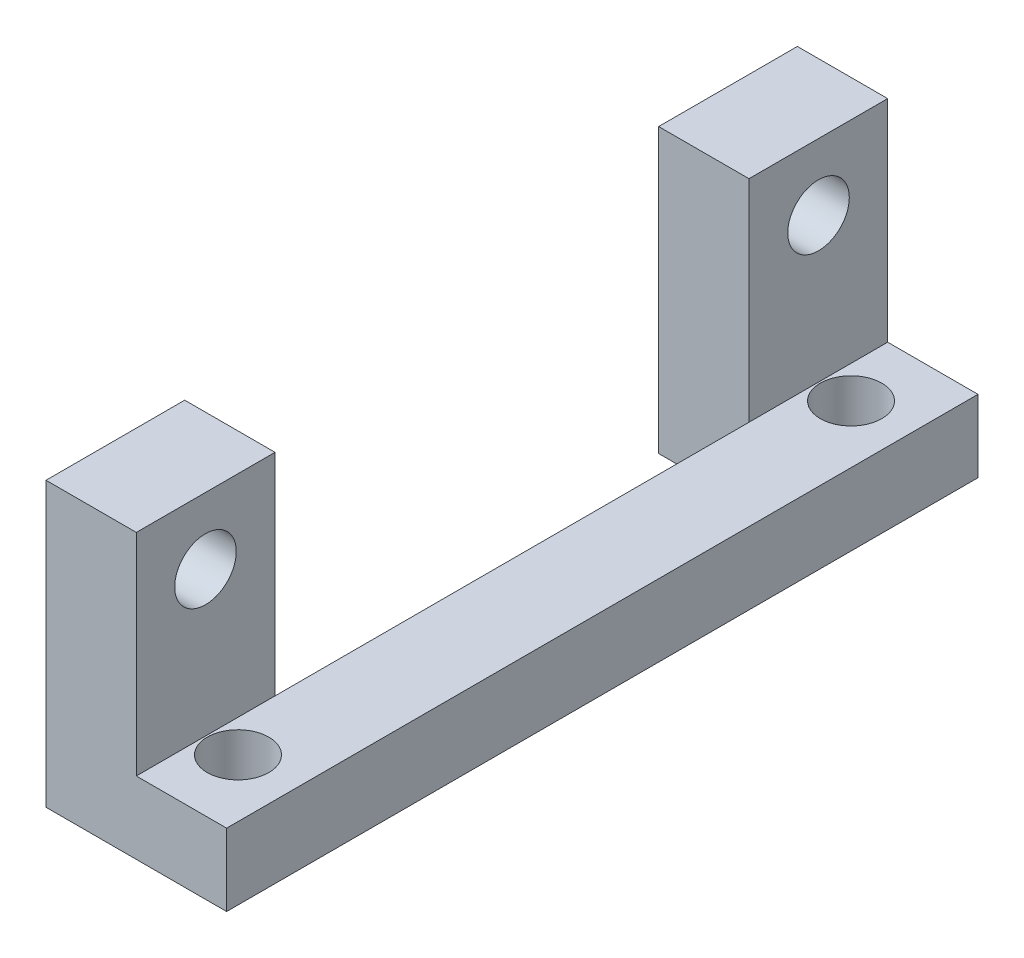
SolidWorks part; units mm, degrees
material "6061 Alloy"
ref_plane "Front Plane" through (0, 0, 0) normal (0, 0, 1) x (1, 0, 0)
ref_plane "Top Plane" through (0, 0, 0) normal (0, 1, 0) x (1, 0, 0)
ref_plane "Right Plane" through (0, 0, 0) normal (1, 0, 0) x (0, 0, -1)
sketch "Sketch1" plane through (0, 0, 0) normal (0, 0, 1) x (1, 0, 0)
  line L0 (0, 12.446) -> (0, 0)
  line L1 (0, 0) -> (7.9375, 0)
  line L2 (7.9375, 0) -> (7.9375, 3.175)
  line L3 (7.9375, 3.175) -> (3.9688, 3.175)
  line L4 (3.9688, 3.175) -> (3.9688, 12.446)
  line L5 (3.9688, 12.446) -> (0, 12.446)
  dimension "D1" = 12.446
  dimension "D2" = 7.9375
  dimension "D3" = 3.9688
  dimension "D4" = 3.175
extrude "Boss-Extrude1" add sketch "Sketch1" along normal mid plane 33.02
sketch "Sketch2" plane through (0, 12.446, 0) normal (0, 1, 0) x (1, 0, 0)
  line L0 (0, -16.51) -> (0, 16.51) construction
  line L1 (0, 10.414) -> (3.9688, 10.414)
  line L2 (0, 10.414) -> (0, -10.414)
  line L3 (0, -10.414) -> (3.9688, -10.414)
  line L4 (3.9688, 10.414) -> (3.9688, -10.414)
  line L5 (3.9688, -16.51) -> (3.9688, 16.51) construction
  dimension "D1" = 20.828
  dimension "D2" = 10.414
extrude "Cut-Extrude1" cut sketch "Sketch2" against normal up to next
hole_wizard "#6-32 Tapped Hole1" positions "Sketch4" profile "Sketch3" tap size "#6-32" standard "Ansi Inch" end condition up to next
sketch "Sketch4" plane through (3.9688, 0, 0) normal (1, 0, 0) x (0, 0, -1)
  line L0 (0, 0) -> (0, 22.9954) construction
  line L1 (0, 22.9954) -> (13.4704, 9.525) construction
  line L2 (0, 22.9954) -> (-13.4704, 9.525) construction
  line L3 (-16.51, 0) -> (16.51, 0) construction
  point P0 (-13.4704, 9.525)
  point P17 (13.4704, 9.525)
  dimension "D1" = 9.525
  dimension "D2" = 19.05
  dimension "D3" = 19.05
sketch "Sketch3" plane through (3.9688, 9.525, 13.4704) normal (0, 1, 0) x (0, 0, -1)
  line L0 (0, 0) -> (0, 3.9688)
  line L1 (0, 3.9688) -> (1.3525, 3.9688)
  line L2 (1.3525, 3.9688) -> (1.3525, 0)
  line L5 (1.3525, 0) -> (0, 0)
  line L11 (0, -6.35) -> (0, 107.95) construction
  dimension "Thread Major Dia." = 2.7051
  dimension "Thru Tap Drill Depth" = 3.9688
hole_wizard "#6-32 Tapped Hole2" positions "Sketch6" profile "Sketch5" tap size "#6-32" standard "Ansi Inch" end condition up to next
sketch "Sketch6" plane through (0, 0, 0) normal (0, -1, 0) x (1, 0, 0)
  line L0 (7.9375, 16.51) -> (7.9375, -16.51) construction
  line L1 (0, 0) -> (27.7345, 0) construction
  line L2 (5.3975, 13.4704) -> (18.8679, 0) construction
  line L3 (5.3975, -13.4704) -> (18.8679, 0) construction
  point P0 (5.3975, 13.4704)
  point P1 (5.3975, -13.4704)
  dimension "D1" = 2.54
  dimension "D2" = 19.05
  dimension "D3" = 19.05
sketch "Sketch5" plane through (5.3975, 0, 13.4704) normal (1, 0, 0) x (0, 0, -1)
  line L0 (0, 0) -> (0, 3.175)
  line L1 (0, 3.175) -> (1.3525, 3.175)
  line L2 (1.3525, 3.175) -> (1.3525, 0)
  line L5 (1.3525, 0) -> (0, 0)
  line L11 (0, -6.35) -> (0, 107.95) construction
  dimension "Thread Major Dia." = 2.7051
  dimension "Thru Tap Drill Depth" = 3.175
